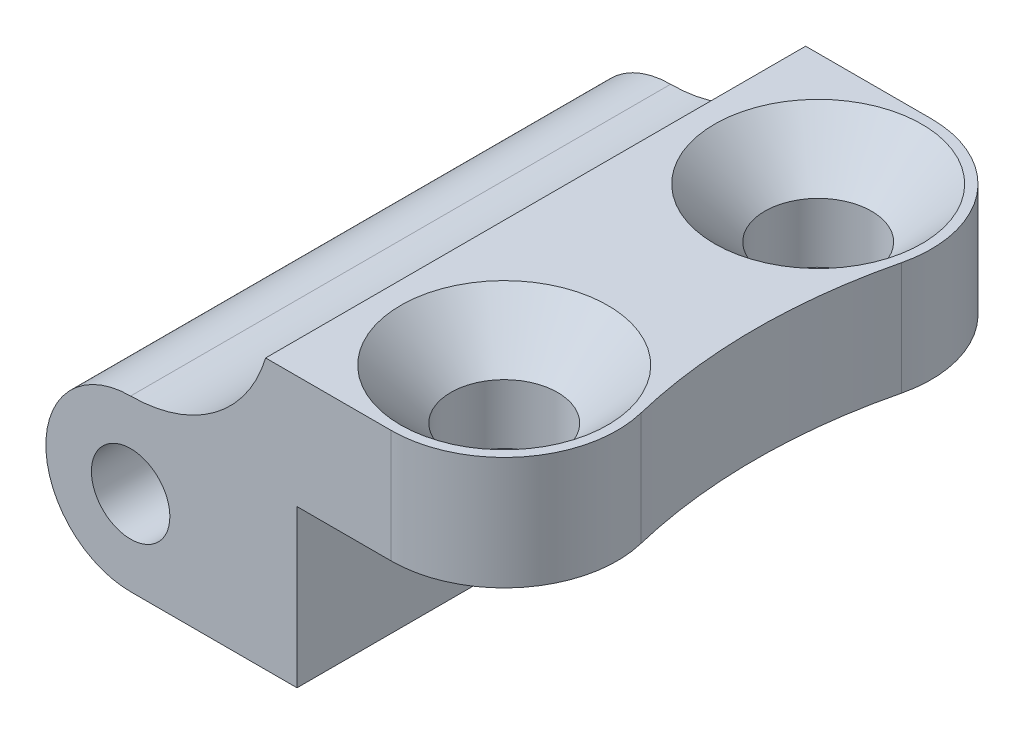
SolidWorks part; units mm, degrees
ref_plane "前视基准面" through (0, 0, 0) normal (0, 0, 1) x (1, 0, 0)
ref_plane "上视基准面" through (0, 0, 0) normal (0, 1, 0) x (1, 0, 0)
ref_plane "右视基准面" through (0, 0, 0) normal (1, 0, 0) x (0, 0, -1)
sketch "草图1" plane through (0, 0, 0) normal (0, 0, 1) x (1, 0, 0)
  line L0 (0, -2.7) -> (5.3, -2.7)
  line L1 (-2.7, 0) -> (-2.7, -2.7) construction
  line L2 (5.3, -2.7) -> (5.3, 2.3)
  line L3 (5.3, 2.3) -> (12.8, 2.3)
  line L4 (12.8, 2.3) -> (12.8, 5.9)
  line L5 (12.8, 5.9) -> (4.3, 5.9)
  circle A0 centre (0, 0) radius 1.25
  arc A1 (0, 2.7) -> (0, -2.7) centre (0, 0) ccw
  arc A2 (0, 2.7) -> (4.3, 5.9) centre (0, 7.1891) ccw
  dimension "D1" = 2.5
  dimension "D2" = 5.4
  dimension "D3" = 8
  dimension "D4" = 5
  dimension "D5" = 7.5
  dimension "D6" = 3.6
  dimension "D7" = 8.5
extrude "凸台-拉伸1" add sketch "草图1" along normal blind 17.2
sketch "草图2" plane through (0, 5.9, 0) normal (0, 1, 0) x (1, 0, 0)
  line L0 (21.5776, -8.6) -> (4.3, -8.6) construction
  line L2 (4.3, -17.2) -> (4.3, 0) construction
  line L3 (8.3, 1.6187) -> (8.3, -20.3658) construction
  line L4 (11.3, -8.6) -> (11.3, -12.8136) construction
  line L5 (12.8, 0) -> (4.3, 0) construction
  line L6 (12.8, -17.2) -> (12.8, 0) construction
  line L7 (12.8, -17.2) -> (4.3, -17.2) construction
  line L8 (12.8, 0) -> (8.3, 0)
  line L9 (12.8, -17.2) -> (12.8, 0)
  line L10 (12.8, -17.2) -> (8.3, -17.2)
  arc A0 (11.7978, -4.4517) -> (11.7978, -12.7483) centre (28.8333, -8.6) ccw
  circle A1 centre (8.3, -3.6) radius 1.5 construction
  circle A2 centre (8.3, -3.6) radius 3.6
  circle A3 centre (8.3, -13.6) radius 1.5 construction
  circle A4 centre (8.3, -13.6) radius 3.6
  line M1 (12.8, 0) -> (4.3, 0)
  line M3 (4.3, -17.2) -> (12.8, -17.2)
  line M4 (12.8, -17.2) -> (12.8, 0)
  dimension "D3" = 3
  dimension "D4" = 7.2
  dimension "D5" = 7
  dimension "D1" = 5
  dimension "D2" = 4
extrude "切除-拉伸1" cut sketch "草图2" against normal through all contours A0 A4 A2 M3 M4 M1
hole_wizard "打孔尺寸(%根据)开槽半沉头木螺钉的类型1" positions "3D草图1" profile "草图3" countersink size "M3" standard "GB"
sketch3d "3D草图1"
  point P0 (8.3, 5.9, 3.6)
  point P3 (8.3, 5.9, 13.6)
sketch "草图3" plane through (8.3, 5.9, 3.6) normal (1, 0, 0) x (0, 0, 1)
  line L0 (0, 0) -> (0, 4.5215)
  line L1 (0, 4.5215) -> (1.7, 3.5)
  line L2 (1.7, 3.5) -> (1.7, 1.6)
  line L3 (1.7, 1.6) -> (3.3, 0)
  line L5 (3.3, 0) -> (0, 0)
  line L6 (-1.7, 1.6) -> (-3.3, 0) construction
  line L10 (0, 4.5215) -> (-1.7, 3.5) construction
  line L11 (0, -6.35) -> (0, 107.95) construction
  dimension "孔直径" = 3.4
  dimension "孔深度" = 3.5
  dimension "近端锥形沉头孔直径" = 6.6
  dimension "近端锥形沉头孔角度" = 90
  dimension "导头角度" = 118
ref_plane "基准面1" through (0, 0, 6) normal (0, 0, 1) x (1, 0, 0)
sketch "草图4" plane through (0, 0, 6) normal (0, 0, 1) x (1, 0, 0)
  line L0 (5.3, -2.7) -> (5.3, 2.3) construction
  line L1 (5.3, 2.3) -> (8.3, 2.3) construction
  line L2 (5.3, -0.5284) -> (5.3, 2.3)
  line L3 (5.3, 2.3) -> (8.1284, 2.3)
  line L4 (8.1284, 2.3) -> (5.3, -0.5284)
  dimension "D1" = 4
extrude "凸台-拉伸2" [suppressed] add sketch "草图4" along normal blind 4
ref_plane "基准面2" through (0, 0, 7.4) normal (0, 0, 1) x (1, 0, 0)
sketch "草图5" plane through (0, 0, 7.4) normal (0, 0, 1) x (1, 0, 0)
  line L3 (5.3, 2.3) -> (5.3, -0.5284)
  line L4 (8.1284, 2.3) -> (5.3, 2.3)
  line L5 (5.3, -0.5284) -> (8.1284, 2.3)
  line L6 (5.3, 2.3) -> (5.3, -0.5284)
  line L7 (8.1284, 2.3) -> (5.3, 2.3)
  line L8 (5.3, -0.5284) -> (8.1284, 2.3)
  dimension "D1" = 0
extrude "凸台-拉伸3" add sketch "草图5" along normal blind 4
